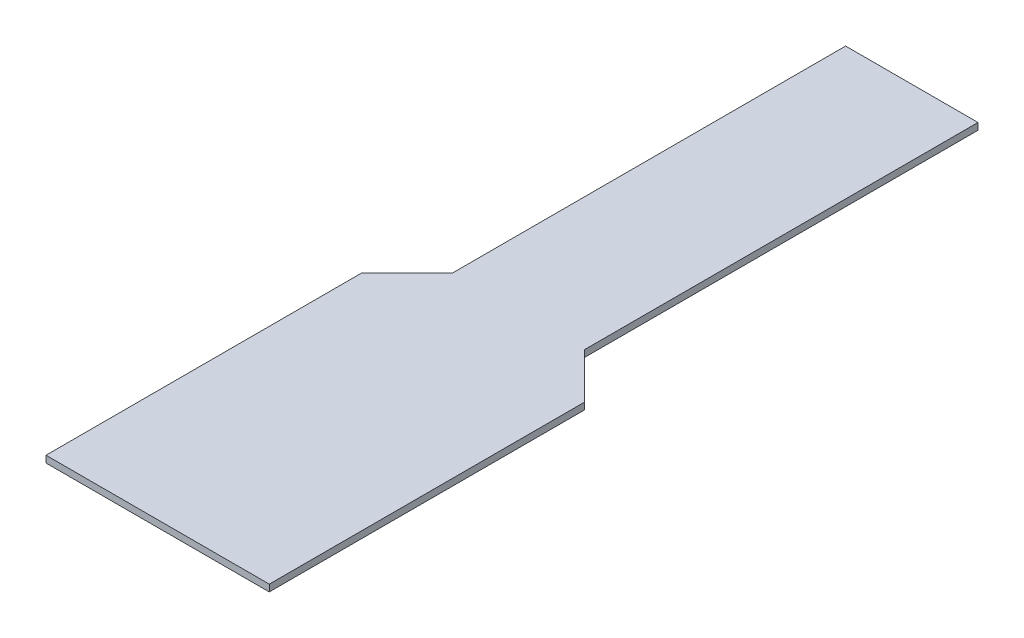
SolidWorks part; units mm, degrees
ref_plane "Front Plane" through (0, 0, 0) normal (0, 0, 1) x (1, 0, 0)
ref_plane "Top Plane" through (0, 0, 0) normal (0, 1, 0) x (1, 0, 0)
ref_plane "Right Plane" through (0, 0, 0) normal (1, 0, 0) x (0, 0, -1)
sketch "Sketch1" plane through (0, 0, 0) normal (0, 1, 0) x (1, 0, 0)
  line L0 (0, 0) -> (0, -73.1358) construction
  line L1 (-6.1976, 0) -> (6.1976, 0)
  line L2 (6.1976, 0) -> (6.1976, -36.83)
  line L3 (6.1976, -36.83) -> (10.4521, -41.0845)
  line L4 (10.4521, -41.0845) -> (10.4521, -70.612)
  line L5 (10.4521, -70.612) -> (-10.4521, -70.612)
  line L6 (-10.4521, -41.0845) -> (-10.4521, -70.612)
  line L7 (-6.1976, -36.83) -> (-10.4521, -41.0845)
  line L8 (-6.1976, 0) -> (-6.1976, -36.83)
  point P9 (0, -70.612)
  dimension "D1" = 70.612
  dimension "D2" = 12.3952
  dimension "D3" = 20.9042
  dimension "D4" = 36.83
  dimension "D5" = 45
extrude "Boss-Extrude1" add sketch "Sketch1" along normal blind 0.635
